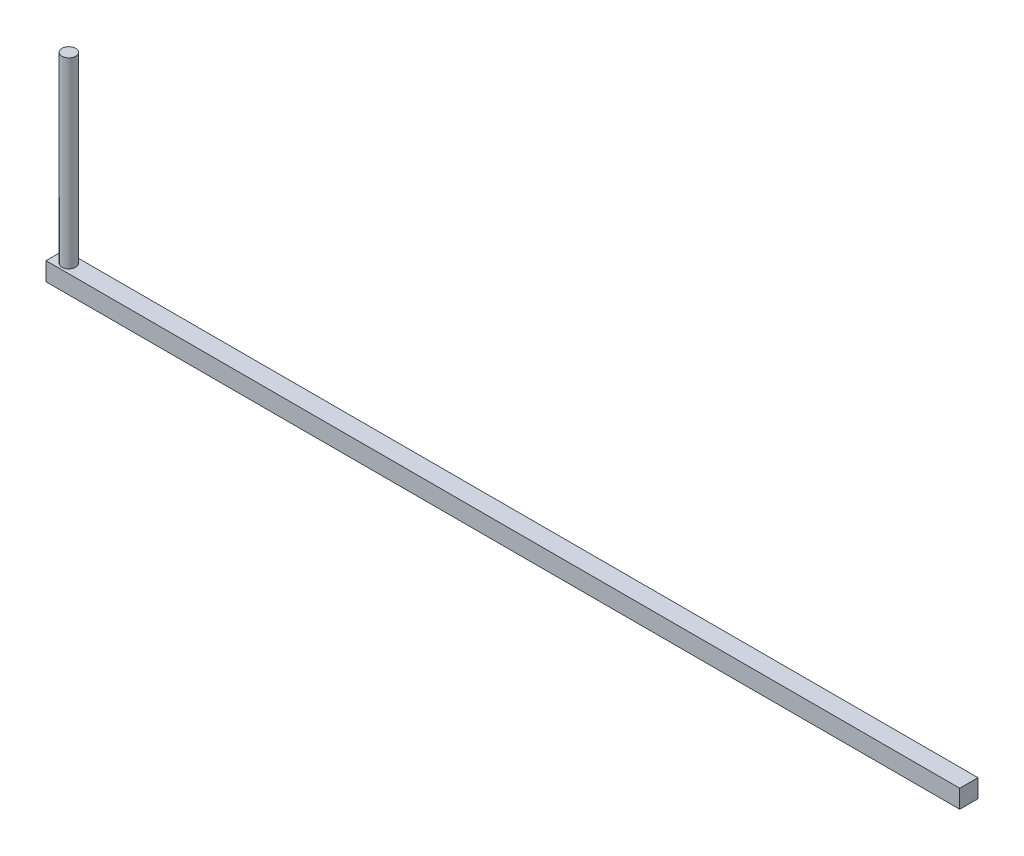
SolidWorks part; units mm, degrees
ref_plane "Front Plane" through (0, 0, 0) normal (0, 0, 1) x (1, 0, 0)
ref_plane "Top Plane" through (0, 0, 0) normal (0, 1, 0) x (1, 0, 0)
ref_plane "Right Plane" through (0, 0, 0) normal (1, 0, 0) x (0, 0, -1)
sketch "Sketch1" plane through (0, 0, 0) normal (0, 1, 0) x (1, 0, 0)
  line L1 (-500, 10) -> (500, 10)
  line L2 (-500, 10) -> (-500, -10)
  line L3 (-500, -10) -> (500, -10)
  line L4 (500, 10) -> (500, -10)
  point P4 (0, 10)
  point P6 (-500, 0)
  dimension "D1" = 20
  dimension "D2" = 1000
extrude "Boss-Extrude1" add sketch "Sketch1" along normal blind 20
sketch "Sketch2" plane through (0, 20, 0) normal (0, 1, 0) x (1, 0, 0)
  line L0 (-500, 10) -> (-500, -10) construction
  line L1 (500, 10) -> (-500, 10) construction
  circle A0 centre (-485, 0) radius 7.5
  dimension "D1" = 15
  dimension "D2" = 15
  dimension "D3" = 10
extrude "Boss-Extrude2" add sketch "Sketch2" along normal blind 200
